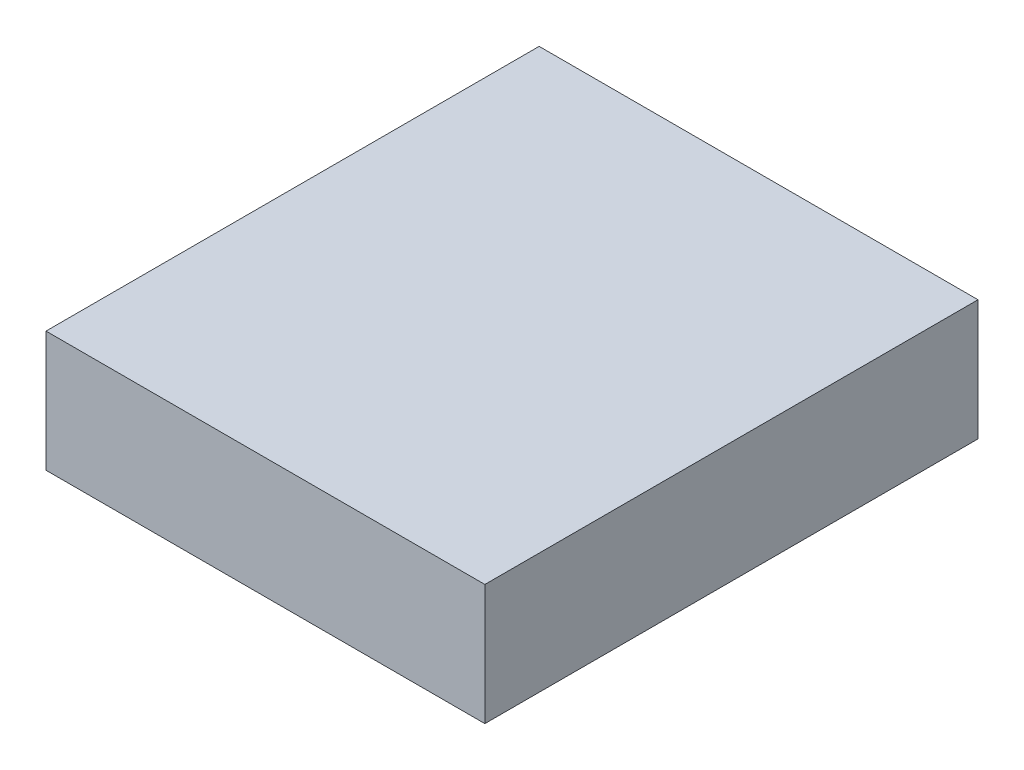
SolidWorks part; units mm, degrees
ref_plane "Front Plane" through (0, 0, 0) normal (0, 0, 1) x (1, 0, 0)
ref_plane "Top Plane" through (0, 0, 0) normal (0, 1, 0) x (1, 0, 0)
ref_plane "Right Plane" through (0, 0, 0) normal (1, 0, 0) x (0, 0, -1)
sketch "Sketch1" plane through (0, 0, 0) normal (0, 1, 0) x (1, 0, 0)
  line L1 (-42.05, 47.25) -> (42.05, 47.25)
  line L2 (-42.05, 47.25) -> (-42.05, -47.25)
  line L3 (-42.05, -47.25) -> (42.05, -47.25)
  line L4 (42.05, 47.25) -> (42.05, -47.25)
  dimension "D1" = 94.5
  dimension "D2" = 84.1
  dimension "D3" = 47.25
  dimension "D4" = 42.05
extrude "Boss-Extrude1" add sketch "Sketch1" along normal mid plane 23.1
